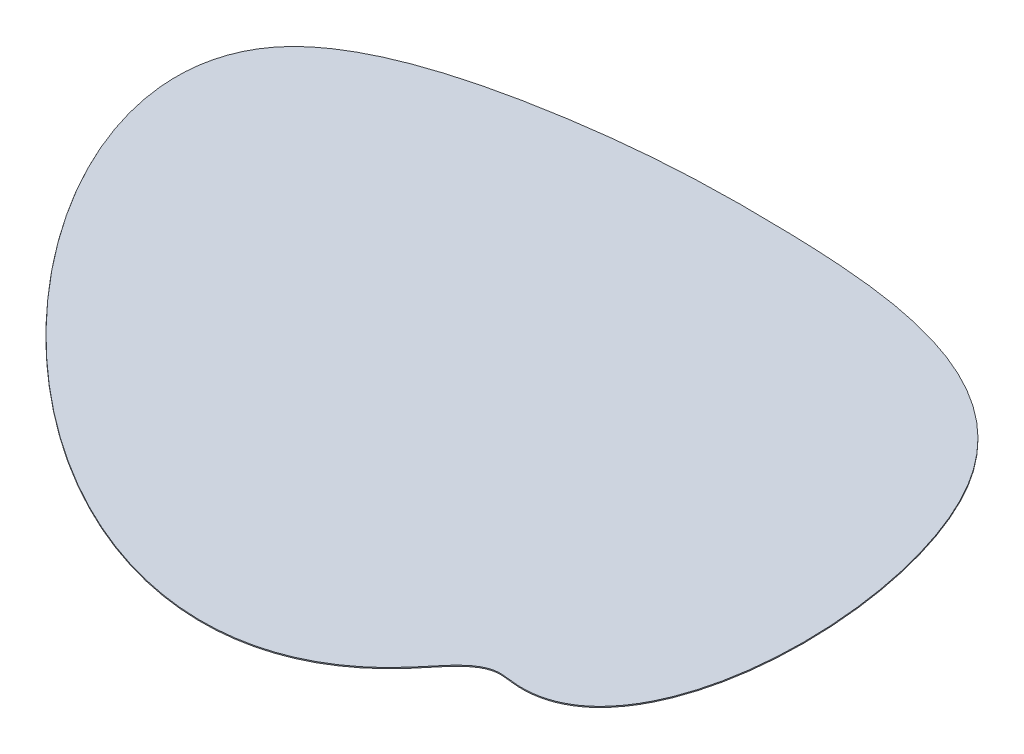
SolidWorks part; units mm, degrees
ref_plane "前视基准面" through (0, 0, 0) normal (0, 0, 1) x (1, 0, 0)
ref_plane "上视基准面" through (0, 0, 0) normal (0, 1, 0) x (1, 0, 0)
ref_plane "右视基准面" through (0, 0, 0) normal (1, 0, 0) x (0, 0, -1)
sketch "草图1" plane through (0, 0, 0) normal (0, 1, 0) x (1, 0, 0)
  spline S0 degree 3 poles (-2053.0172, 2727.0916) (256.5755, 2810.949) (3840.8011, 2436.6982) (3779.9939, -2678.6997) (2134.206, -2380.4522) (1017.3506, -4130.0417) (-2858.2068, -2681.2625) (-5353.8841, 1853.3636) (-2053.0172, 2727.0916) (256.5755, 2810.949) (3840.8011, 2436.6982) knots -0.405016 -0.203271 -0.105407 0 0.15506 0.346397 0.353891 0.383559 0.594984 0.796729 0.894593 1 1.15506 1.346397 1.353891 only from (0, 2754.012) to (0, 2754.012)
  point P0 (0, 0)
  point P6 (0, 0)
  point P9 (-3516.8119, 1118.0418)
  point P11 (0, 3000)
  point P14 (-904.143, -2129.4813)
  point P16 (3222.4089, 1667.4348)
  point P18 (2453.8618, -2434.288)
  point P20 (1818.4046, -2813.1704)
  point P21 (-4090.6224, 1862.7745)
  point P22 (0, 2754.012)
  point P23 (2990.443, 1520.93)
  point P24 (0, 0)
extrude "凸台-拉伸1" add sketch "草图1" along normal blind 10
